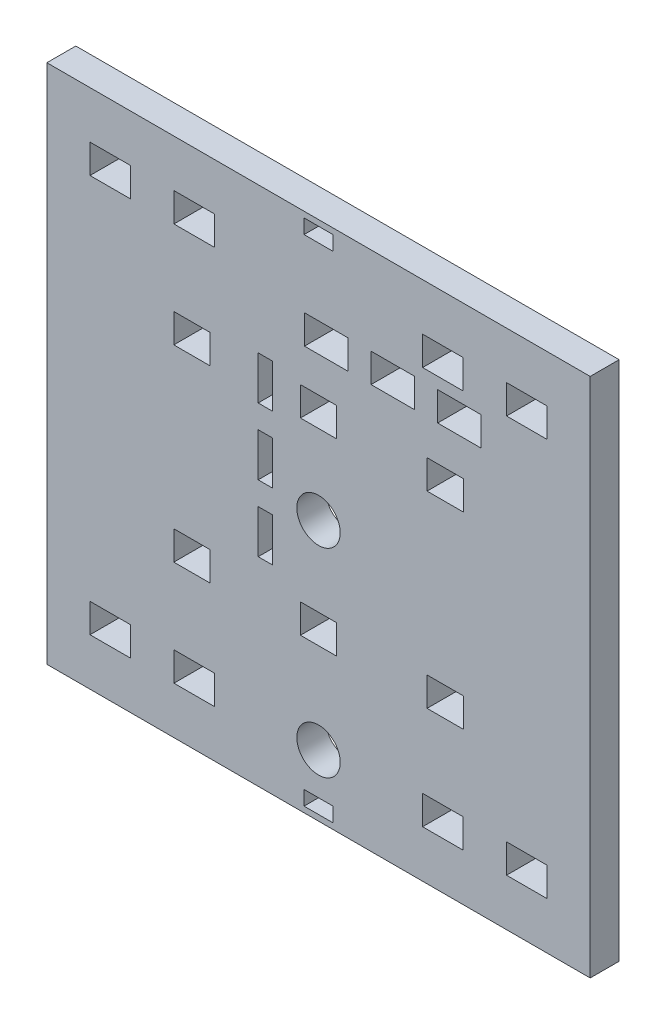
SolidWorks part; units mm, degrees
ref_plane "Front Plane" through (0, 0, 0) normal (0, 0, 1) x (1, 0, 0)
ref_plane "Top Plane" through (0, 0, 0) normal (0, 1, 0) x (1, 0, 0)
ref_plane "Right Plane" through (0, 0, 0) normal (1, 0, 0) x (0, 0, -1)
sketch "Sketch1" plane through (0, 0, 0) normal (0, 0, 1) x (1, 0, 0)
  line L0 (-93.9544, 90) -> (93.9544, -90) construction
  line L1 (-93.9544, 90) -> (93.9544, 90)
  line L2 (-93.9544, 90) -> (-93.9544, -90)
  line L3 (-93.9544, -90) -> (93.9544, -90)
  line L4 (93.9544, 90) -> (93.9544, -90)
  line L5 (93.9544, -90) -> (93.9544, 90) construction
  line L6 (93.9544, 90) -> (0, 0) construction
  line L7 (0, 0) -> (-93.9544, -90) construction
  line L8 (0, 88) -> (0, 83) construction
  line L9 (35.9544, -73.7) -> (49.9544, -73.7)
  line L10 (35.9544, 73.7) -> (49.9544, 73.7)
  line L11 (35.9544, 73.7) -> (35.9544, 63.7)
  line L12 (35.9544, 63.7) -> (49.9544, 63.7)
  line L13 (49.9544, 73.7) -> (49.9544, 63.7)
  line L14 (64.9544, 73.7) -> (78.9544, 73.7)
  line L15 (64.9544, 73.7) -> (64.9544, 63.7)
  line L16 (64.9544, 63.7) -> (78.9544, 63.7)
  line L17 (78.9544, 73.7) -> (78.9544, 63.7)
  line L18 (35.9544, -63.7) -> (49.9544, -63.7)
  line L19 (0, 90) -> (0, -90) construction
  line L20 (35.9544, -73.7) -> (35.9544, -63.7)
  line L21 (49.9544, -73.7) -> (49.9544, -63.7)
  line L22 (64.9544, -63.7) -> (78.9544, -63.7)
  line L23 (64.9544, -73.7) -> (64.9544, -63.7)
  line L24 (64.9544, -73.7) -> (78.9544, -73.7)
  line L25 (78.9544, -73.7) -> (78.9544, -63.7)
  line L26 (-78.9544, -73.7) -> (-78.9544, -63.7)
  line L27 (-64.9544, -63.7) -> (-78.9544, -63.7)
  line L28 (-64.9544, -73.7) -> (-64.9544, -63.7)
  line L29 (-64.9544, -73.7) -> (-78.9544, -73.7)
  line L30 (-49.9544, -73.7) -> (-49.9544, -63.7)
  line L31 (-35.9544, -73.7) -> (-35.9544, -63.7)
  line L32 (-35.9544, -63.7) -> (-49.9544, -63.7)
  line L33 (-35.9544, -73.7) -> (-49.9544, -73.7)
  line L34 (-35.9544, 63.7) -> (-49.9544, 63.7)
  line L35 (-35.9544, 73.7) -> (-35.9544, 63.7)
  line L36 (-15.85, 90) -> (-15.85, -90) construction
  line L37 (-20.85, 90) -> (-20.85, -90) construction
  line L38 (93.9544, -6.3) -> (-93.9544, -6.3) construction
  line L39 (-20.85, -90) -> (-20.85, -6.3) construction
  line L40 (-20.85, -6.3) -> (-15.85, -6.3) construction
  line L41 (-93.9544, 49.7) -> (93.9544, 49.7) construction
  line L42 (-20.85, -6.3) -> (-15.85, -6.3)
  line L43 (-20.85, -6.3) -> (-20.85, -21.3)
  line L44 (-20.85, -21.3) -> (-15.85, -21.3)
  line L45 (-15.85, -6.3) -> (-15.85, -21.3)
  line L46 (-20.85, 1.7) -> (-15.85, 1.7)
  line L47 (-20.85, 1.7) -> (-20.85, 16.7)
  line L48 (-20.85, 16.7) -> (-15.85, 16.7)
  line L49 (-15.85, 1.7) -> (-15.85, 16.7)
  line L50 (-20.85, 24.7) -> (-15.85, 24.7)
  line L51 (-20.85, 24.7) -> (-20.85, 39.7)
  line L52 (-20.85, 39.7) -> (-15.85, 39.7)
  line L53 (-15.85, 24.7) -> (-15.85, 39.7)
  line L54 (-93.9544, 59.7) -> (93.9544, 59.7) construction
  line L55 (-4.85, 90) -> (-4.85, -90) construction
  line L56 (-4.85, 90) -> (-4.85, 59.7) construction
  line L57 (-4.85, 59.7) -> (-4.85, 49.7) construction
  line L58 (-93.9544, 88) -> (93.9544, 88) construction
  line L59 (-4.85, 59.7) -> (10.15, 59.7)
  line L60 (-4.85, 59.7) -> (-4.85, 49.7)
  line L61 (-4.85, 49.7) -> (10.15, 49.7)
  line L62 (10.15, 59.7) -> (10.15, 49.7)
  line L63 (18.15, 49.7) -> (33.15, 49.7)
  line L64 (18.15, 49.7) -> (18.15, 59.7)
  line L65 (18.15, 59.7) -> (33.15, 59.7)
  line L66 (33.15, 49.7) -> (33.15, 59.7)
  line L67 (41.15, 49.7) -> (56.15, 49.7)
  line L68 (41.15, 49.7) -> (41.15, 59.7)
  line L69 (41.15, 59.7) -> (56.15, 59.7)
  line L70 (56.15, 49.7) -> (56.15, 59.7)
  line L71 (0, 0) -> (93.9544, 0) construction
  line L72 (-5, 88) -> (5, 88)
  line L73 (-5, 88) -> (-5, 83)
  line L74 (-5, 83) -> (5, 83)
  line L75 (5, 88) -> (5, 83)
  line L76 (-5, -88) -> (5, -88)
  line L77 (5, -88) -> (5, -83)
  line L78 (-5, -88) -> (-5, -83)
  line L79 (-5, -83) -> (5, -83)
  line L80 (-35.9544, 73.7) -> (-49.9544, 73.7)
  line L81 (-49.9544, 73.7) -> (-49.9544, 63.7)
  line L82 (-64.9544, 63.7) -> (-78.9544, 63.7)
  line L83 (-64.9544, 73.7) -> (-64.9544, 63.7)
  line L84 (-64.9544, 73.7) -> (-78.9544, 73.7)
  line L85 (-78.9544, 73.7) -> (-78.9544, 63.7)
  line L86 (42.9544, 73.7) -> (42.9544, 90) construction
  line L87 (-93.9544, 32.5) -> (-50, 32.5) construction
  line L88 (-50, 37.5) -> (-37.5, 37.5)
  line L89 (-50, 37.5) -> (-50, 27.5)
  line L90 (-50, 27.5) -> (-37.5, 27.5)
  line L91 (-37.5, 37.5) -> (-37.5, 27.5)
  line L92 (-6.25, 37.5) -> (6.25, 37.5)
  line L93 (-6.25, 37.5) -> (-6.25, 27.5)
  line L94 (-6.25, 27.5) -> (6.25, 27.5)
  line L95 (6.25, 37.5) -> (6.25, 27.5)
  line L96 (37.5, 37.5) -> (50, 37.5)
  line L97 (37.5, 37.5) -> (37.5, 27.5)
  line L98 (37.5, 27.5) -> (50, 27.5)
  line L99 (50, 37.5) -> (50, 27.5)
  line L100 (-50, 32.5) -> (-37.5, 32.5) construction
  line L101 (-37.5, 32.5) -> (-6.25, 32.5) construction
  line L102 (-6.25, 32.5) -> (6.25, 32.5) construction
  line L103 (6.25, 32.5) -> (37.5, 32.5) construction
  line L104 (37.5, 32.5) -> (50, 32.5) construction
  line L105 (50, 32.5) -> (93.9544, 32.5) construction
  line L106 (-50, -27.5) -> (-37.5, -27.5)
  line L107 (-50, -37.5) -> (-50, -27.5)
  line L108 (-50, -37.5) -> (-37.5, -37.5)
  line L109 (-37.5, -37.5) -> (-37.5, -27.5)
  line L110 (-6.25, -27.5) -> (6.25, -27.5)
  line L111 (-6.25, -37.5) -> (-6.25, -27.5)
  line L112 (-6.25, -37.5) -> (6.25, -37.5)
  line L113 (6.25, -37.5) -> (6.25, -27.5)
  line L114 (37.5, -27.5) -> (50, -27.5)
  line L115 (37.5, -37.5) -> (37.5, -27.5)
  line L116 (37.5, -37.5) -> (50, -37.5)
  line L117 (50, -37.5) -> (50, -27.5)
  line L118 (-93.8544, 90) -> (-93.8544, -90)
  line L119 (93.8544, 90) -> (93.8544, -90)
  line L120 (-35.9544, -68.7) -> (0, -68.7) construction
  line L121 (0, -68.7) -> (35.9544, -68.7) construction
  circle A0 centre (0, -68.7) radius 7.5
  circle A1 centre (0, 0) radius 7.5
  dimension "D29" = 15
  dimension "D30" = 15
  dimension "D1" = 187.9087
  dimension "D2" = 180
  dimension "D3" = 10
  dimension "D4" = 14
  dimension "D5" = 4
  dimension "D6" = 15
  dimension "D7" = 15
  dimension "D8" = 127.4
  dimension "D9" = 15.85
  dimension "D10" = 5
  dimension "D11" = 6.3
  dimension "D12" = 15
  dimension "D13" = 8
  dimension "D14" = 8
  dimension "D15" = 49.7
  dimension "D16" = 10
  dimension "D17" = 4.85
  dimension "D18" = 8
  dimension "D19" = 8
  dimension "D20" = 15
  dimension "D21" = 2
  dimension "D22" = 5
  dimension "D23" = 10
  dimension "D24" = 57.5
  dimension "D25" = 10
  dimension "D26" = 100
  dimension "D27" = 12.5
  dimension "D28" = 0.1
extrude "Boss-Extrude1" add sketch "Sketch1" along normal blind 10
